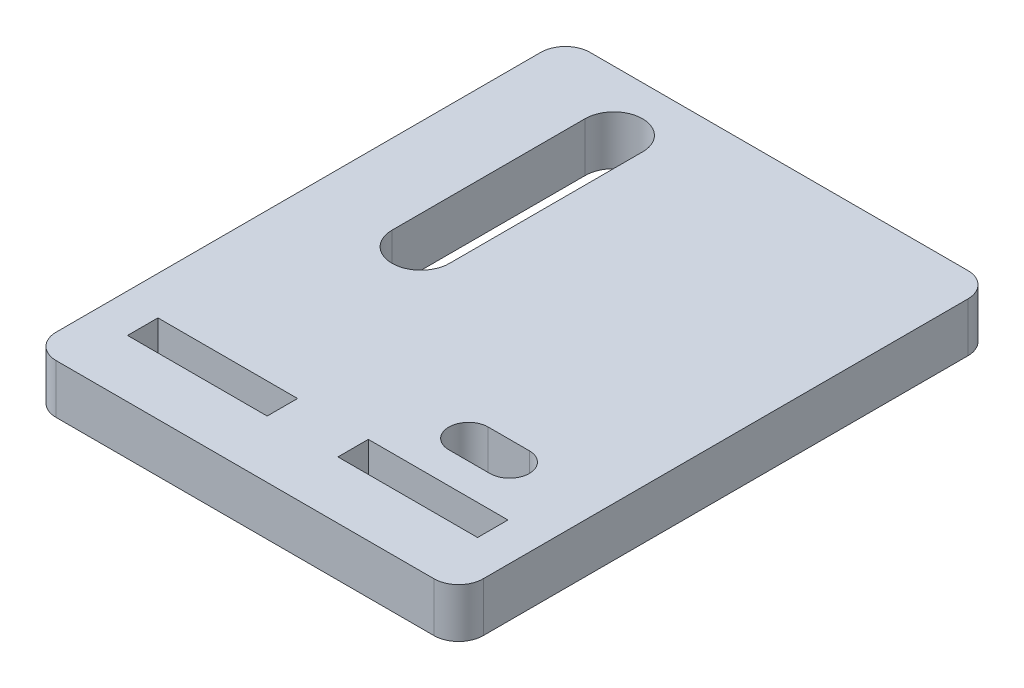
SolidWorks part; units mm, degrees
ref_plane "Front Plane" through (0, 0, 0) normal (0, 0, 1) x (1, 0, 0)
ref_plane "Top Plane" through (0, 0, 0) normal (0, 1, 0) x (1, 0, 0)
ref_plane "Right Plane" through (0, 0, 0) normal (1, 0, 0) x (0, 0, -1)
sketch "Sketch1" plane through (0, 0, 0) normal (0, 1, 0) x (1, 0, 0)
  line L1 (-26, -32.5) -> (26, -32.5)
  line L2 (-26, -32.5) -> (-26, 32.5)
  line L3 (-26, 32.5) -> (26, 32.5)
  line L4 (26, -32.5) -> (26, 32.5)
  line L5 (-26, -32.5) -> (26, 32.5) construction
  line L6 (-26, 32.5) -> (26, -32.5) construction
  point P0 (0, 0)
  dimension "D1" = 52
  dimension "D2" = 65
extrude "Boss-Extrude1" add sketch "Sketch1" along normal blind 6
fillet "Fillet1" radius 3 4 edges at (-26, 3, -32.5) (26, 3, 32.5) (26, 3, -32.5) (-26, 3, 32.5)
sketch "Sketch4" plane through (0, 6, 0) normal (0, 1, 0) x (1, 0, 0)
  line L0 (12.8078, -23.65) -> (-12.8078, -23.65) construction
  line L1 (-23, -32.5) -> (23, -32.5) construction
  line L2 (-21.3078, -25.5) -> (-4.3078, -25.5)
  line L3 (-21.3078, -25.5) -> (-21.3078, -21.8)
  line L4 (-21.3078, -21.8) -> (-4.3078, -21.8)
  line L5 (-4.3078, -25.5) -> (-4.3078, -21.8)
  line L6 (-21.3078, -25.5) -> (-4.3078, -21.8) construction
  line L7 (-21.3078, -21.8) -> (-4.3078, -25.5) construction
  point P3 (0, -23.65)
  point P7 (19.1631, -19.614)
  point P8 (0, 0)
  point P10 (13.3946, -19.5795)
  dimension "D1" = 3.7
  dimension "D2" = 17
  dimension "D3" = 7
extrude "Cut-Extrude1" cut sketch "Sketch4" against normal through all
mirror "Mirror2" about plane through (0, 0, 0) normal (1, 0, 0) of "Cut-Extrude1"
sketch "Sketch5" plane through (0, 6, 0) normal (0, 1, 0) x (1, 0, 0)
  line L0 (10.3078, -15.6) -> (15.3078, -15.6) construction
  line L1 (10.3078, -13.2) -> (15.3078, -13.2)
  line L2 (10.3078, -18) -> (15.3078, -18)
  line L3 (4.3078, -21.8) -> (21.3078, -21.8) construction
  arc A0 (10.3078, -13.2) -> (10.3078, -18) centre (10.3078, -15.6) ccw
  arc A1 (15.3078, -18) -> (15.3078, -13.2) centre (15.3078, -15.6) ccw
  point P2 (12.8078, -15.6)
  point P7 (12.8078, -13.2)
  point P10 (0, 0)
  point P11 (12.6548, -15.6)
  point P12 (12.8078, -21.8)
  dimension "D1" = 5
  dimension "D2" = 4.8
  dimension "D3" = 6.2
extrude "Cut-Extrude2" cut sketch "Sketch5" against normal through all
sketch "Sketch6" plane through (0, 6, 0) normal (0, 1, 0) x (1, 0, 0)
  line L0 (-12.8078, 25.2) -> (-12.8078, 1.7) construction
  line L1 (-9.3078, 25.2) -> (-9.3078, 1.7)
  line L2 (-16.3078, 25.2) -> (-16.3078, 1.7)
  line L3 (-4.3078, -21.8) -> (-21.3078, -21.8) construction
  arc A0 (-9.3078, 25.2) -> (-16.3078, 25.2) centre (-12.8078, 25.2) ccw
  arc A1 (-16.3078, 1.7) -> (-9.3078, 1.7) centre (-12.8078, 1.7) ccw
  point P2 (-12.8078, 13.45)
  point P7 (-15.1995, 2.6044)
  point P10 (-12.8078, -1.8)
  point P11 (-12.8078, 28.7)
  point P12 (-12.8078, -21.8)
  dimension "D1" = 20
  dimension "D2" = 50.5
  dimension "D3" = 7
extrude "Cut-Extrude3" cut sketch "Sketch6" against normal through all
